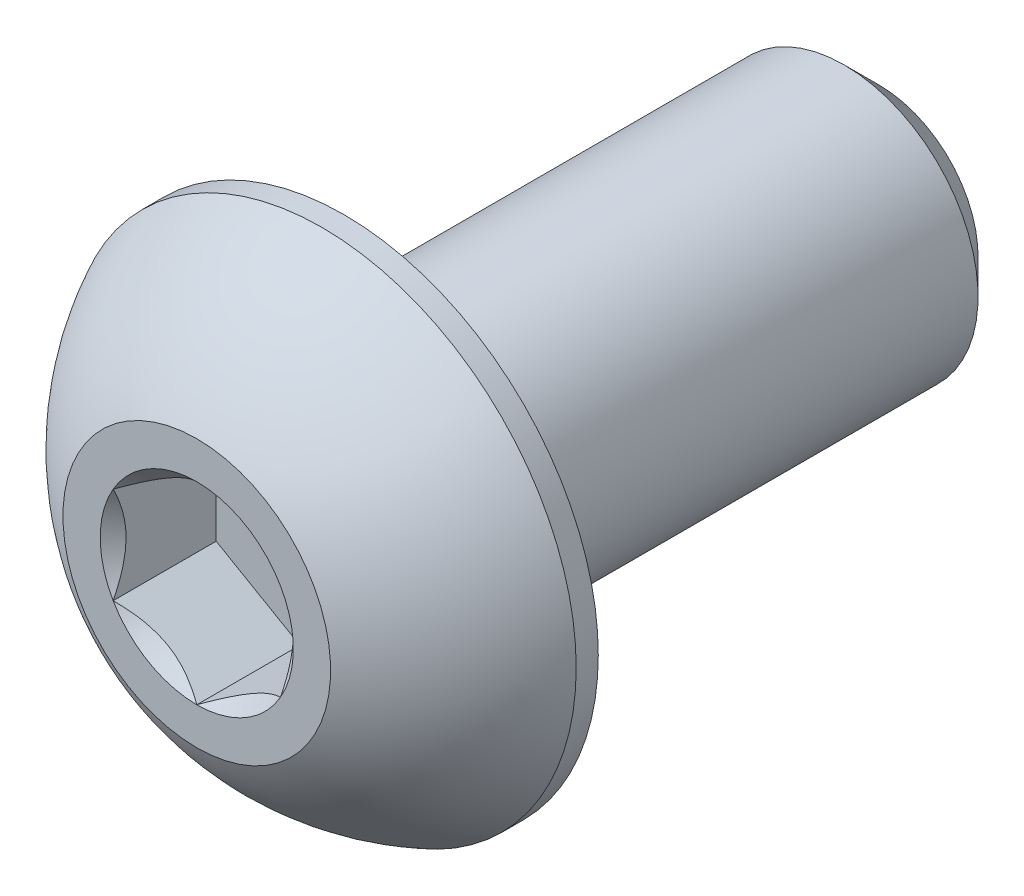
SolidWorks part; units mm, degrees
ref_plane "Front" through (0, 0, 0) normal (0, 0, 1) x (1, 0, 0)
ref_plane "Top" through (0, 0, 0) normal (0, 1, 0) x (1, 0, 0)
ref_plane "Right" through (0, 0, 0) normal (1, 0, 0) x (0, 0, -1)
sketch "Sketch1" plane through (0, 0, 0) normal (1, 0, 0) x (0, 0, -1)
  line L2 (2.2, 2) -> (10.2, 2)
  line L3 (10.2, 2) -> (10.2, 0)
  line L4 (10.2, 0) -> (2.2, 0)
  line L6 (1.87, 3.8) -> (2.2, 3.8) construction
  line L7 (10.2, 2) -> (10.2, -2) construction
  line L8 (0, 0) -> (2.2, 0) construction
  line L9 (2.2, 3.8) -> (2.2, -3.8) construction
  line L11 (2.2, 2) -> (2.2, 0)
  line L13 (0, 1.25) -> (0, -1.25) construction
  line L14 (0, 1.25) -> (0, 2) construction
  arc A3 (0, 2) -> (1.87, 3.8) centre (3.7264, 0) cw construction
  dimension "D1" = 0.33
revolve "Revolve1" add sketch "Sketch1" angle 360 mid plane about L4
chamfer "Chamfer1" distance 0.525 angle 45 1 edges at (0, 2, -10.2)
sketch "Sketch7" plane through (0, 0, 0) normal (1, 0, 0) x (0, 0, -1)
  line L6 (1.87, 3.8) -> (2.2, 3.8) construction
  line L8 (0, 0) -> (2.2, 0) construction
  line L11 (2.2, 3.8) -> (2.2, -3.8) construction
  line L12 (1.87, 3.8) -> (2.2, 3.8)
  line L13 (0, 0) -> (2.2, 0)
  line L14 (0, 1.25) -> (0, -1.25) construction
  line L15 (2.2, 3.8) -> (2.2, 0)
  line L16 (0, 2) -> (0, 0)
  arc A2 (1.87, 3.8) -> (0, 2) centre (3.7264, 0) ccw construction
  arc A3 (1.87, 3.8) -> (0, 2) centre (3.7264, 0) ccw
revolve "Revolve2" add sketch "Sketch7" angle 360 mid plane about L13
sketch "Sketch5" plane through (0, 0, 0) normal (0, 0, 1) x (1, 0, 0)
  line L1 (1.25, -0.7217) -> (1.25, 0.7217)
  line L2 (1.25, 0.7217) -> (0, 1.4434)
  line L3 (0, 1.4434) -> (-1.25, 0.7217)
  line L4 (-1.25, 0.7217) -> (-1.25, -0.7217)
  line L5 (-1.25, -0.7217) -> (0, -1.4434)
  line L6 (0, -1.4434) -> (1.25, -0.7217)
  circle A0 centre (0, 0) radius 1.25 construction
extrude "Cut-Extrude2" cut sketch "Sketch5" against normal blind 1.54
sketch "Sketch6" plane through (0, 0, 0) normal (0, 0, 1) x (1, 0, 0)
  circle A0 centre (0, 0) radius 1.4434
extrude "Cut-Extrude3" cut sketch "Sketch6" against normal blind 1.54 draft 45
equation "\"D1@Cut-Extrude2\" = \"Head Ht@Sketch1\" * .7"
equation "\"D1@Sketch1\" = \"Head Ht@Sketch1\" * .15"
equation "\"D1@Cut-Extrude3\" = \"D1@Cut-Extrude2\""
